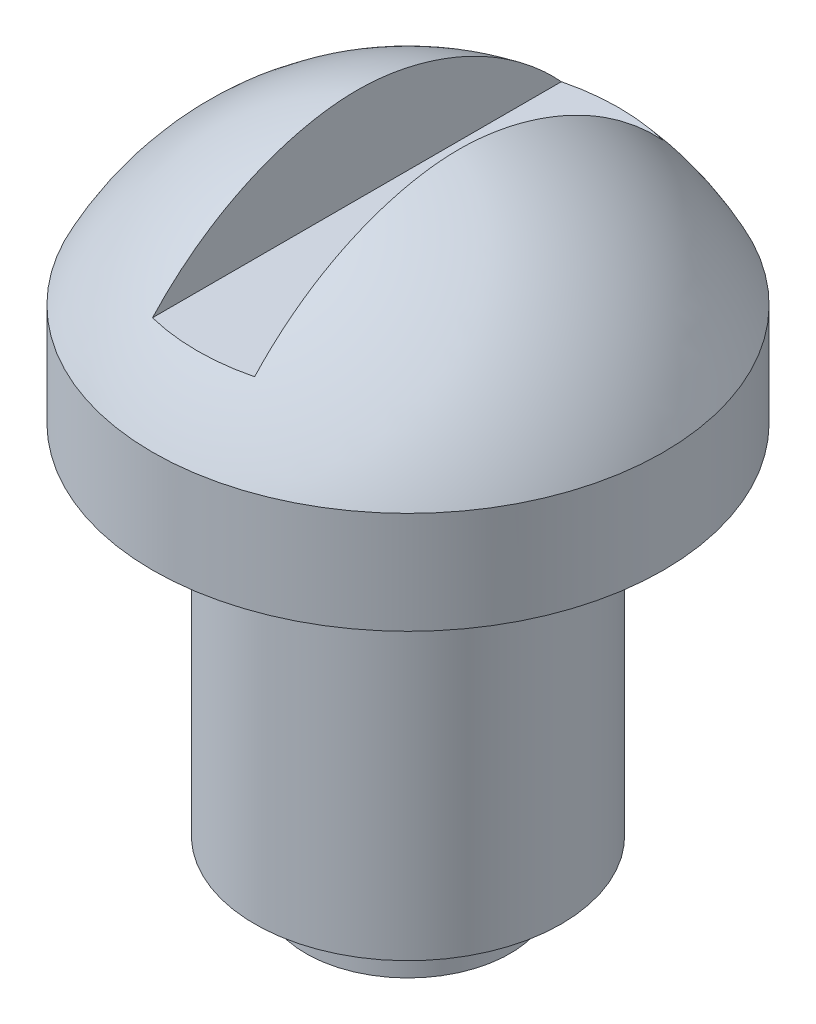
SolidWorks part; units mm, degrees
ref_plane "Front Plane" through (0, 0, 0) normal (0, 0, 1) x (1, 0, 0)
ref_plane "Top Plane" through (0, 0, 0) normal (0, 1, 0) x (1, 0, 0)
ref_plane "Right Plane" through (0, 0, 0) normal (1, 0, 0) x (0, 0, -1)
sketch "Sketch1" plane through (0, 0, 0) normal (0, 0, 1) x (1, 0, 0)
  line L0 (0, 0) -> (2, 0)
  line L1 (2, 0) -> (2, 1)
  line L2 (2, 1) -> (3, 1)
  line L3 (3, 1) -> (3, 8)
  line L4 (3, 8) -> (5, 8)
  line L5 (5, 8) -> (5, 10)
  line L8 (0, 13.2835) -> (0, 0)
  arc A1 (5, 10) -> (0, 13.2835) centre (-0.3551, 7.294) ccw
  point P3 (0, 0)
  point P10 (0, 0)
  point P12 (0, 13.5781)
  point P13 (0, 0)
  point P15 (1.5, 11.0125)
  dimension "D1" = 2
  dimension "D3" = 2
  dimension "D9" = 6
  dimension "D4" = 1
  dimension "D5" = 7
  dimension "D6" = 5
  dimension "D7" = 3
revolve "Revolve1" add sketch "Sketch1" angle 360 about L8
sketch "Sketch2" plane through (0, 0, 0) normal (0, 0, 1) x (1, 0, 0)
  line L1 (1, 11.2835) -> (-1, 11.2835)
  line L2 (1, 11.2835) -> (1, 15.2835)
  line L3 (1, 15.2835) -> (-1, 15.2835)
  line L4 (-1, 11.2835) -> (-1, 15.2835)
  line L5 (1, 11.2835) -> (-1, 15.2835) construction
  line L6 (1, 15.2835) -> (-1, 11.2835) construction
  point P0 (0, 13.2835)
  point P5 (0, 0)
  dimension "D1" = 4
  dimension "D2" = 2
extrude "Cut-Extrude1" cut sketch "Sketch2" against normal through all both and the other way through all
